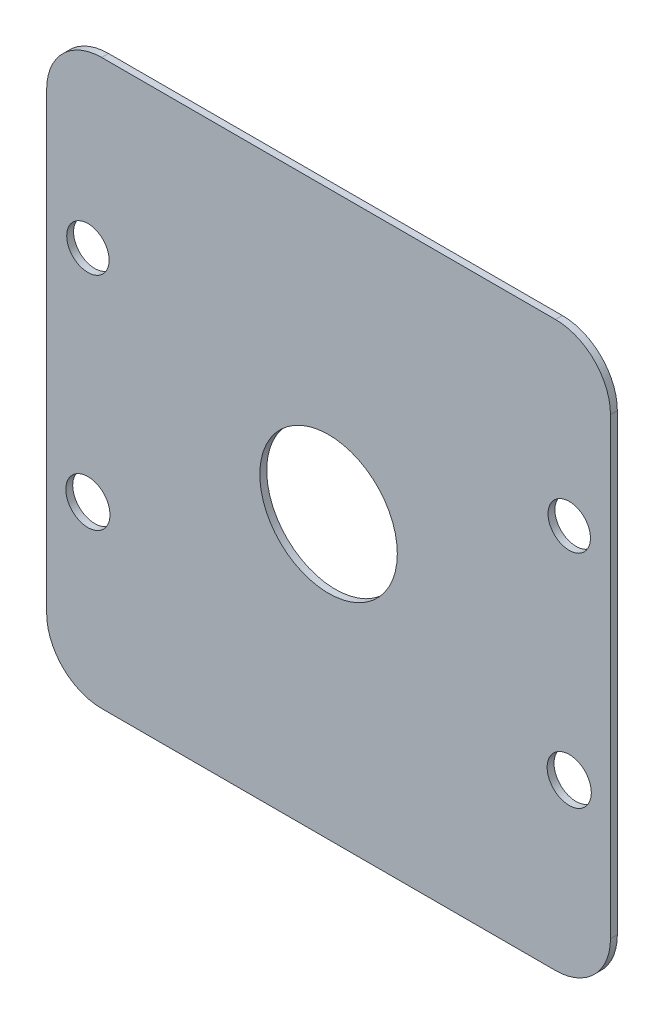
SolidWorks part; units mm, degrees
ref_plane "Plano frontal" through (0, 0, 0) normal (0, 0, 1) x (1, 0, 0)
ref_plane "Plano superior" through (0, 0, 0) normal (0, 1, 0) x (1, 0, 0)
ref_plane "Plano direito" through (0, 0, 0) normal (1, 0, 0) x (0, 0, -1)
sketch "Esboço1" plane through (0, 0, 0) normal (0, 0, 1) x (1, 0, 0)
  line L0 (0, 23.8289) -> (0, -27.123) construction
  line L1 (-16.5, -20.5) -> (16.5, -20.5)
  line L2 (-20.5, -16.5) -> (-20.5, 16.5)
  line L3 (-16.5, 20.5) -> (16.5, 20.5)
  line L4 (20.5, -16.5) -> (20.5, 16.5)
  line L5 (-20.5, -20.5) -> (20.5, 20.5) construction
  line L6 (-20.5, 20.5) -> (20.5, -20.5) construction
  line L7 (17.5, 8) -> (17.5, -8) construction
  arc A0 (-20.5, -16.5) -> (-16.5, -20.5) centre (-16.5, -16.5) ccw
  arc A1 (16.5, -20.5) -> (20.5, -16.5) centre (16.5, -16.5) ccw
  arc A2 (20.5, 16.5) -> (16.5, 20.5) centre (16.5, 16.5) ccw
  arc A3 (-20.5, 16.5) -> (-16.5, 20.5) centre (-16.5, 16.5) cw
  circle A4 centre (0, 0) radius 5
  circle A5 centre (17.5, -8) radius 1.6061
  circle A6 centre (17.5, 8) radius 1.5416
  circle A7 centre (-17.5, 8) radius 1.5416
  circle A8 centre (-17.5, -8) radius 1.6061
  point P0 (0, 0)
  point P30 (20.5, 0)
  point P31 (17.5, 0)
  dimension "D3" = 4
  dimension "D4" = 10
  dimension "D1" = 41
  dimension "D2" = 41
  dimension "D6" = 3
  dimension "D7" = 3
  dimension "D8" = 16
extrude "Ressalto-extrusão1" add sketch "Esboço1" along normal blind 0.5
